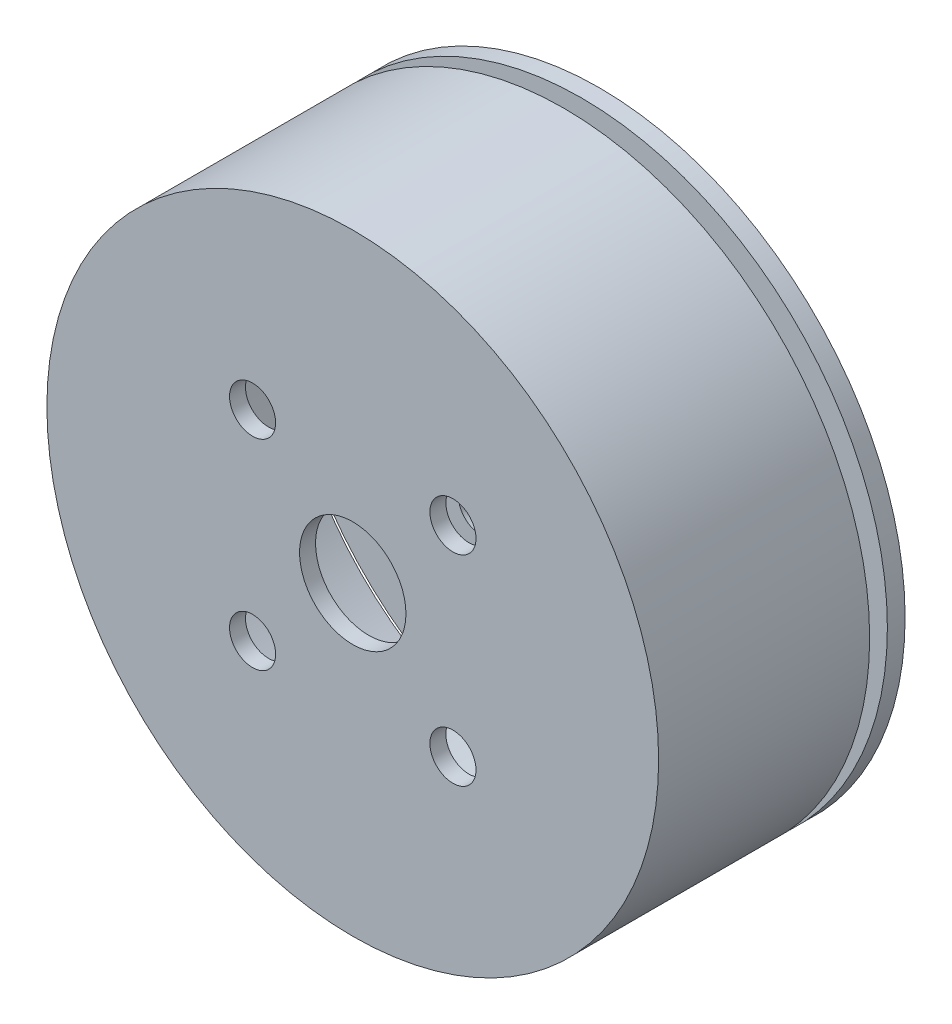
SolidWorks part; units mm, degrees
ref_plane "前视基准面" through (0, 0, 0) normal (0, 0, 1) x (1, 0, 0)
ref_plane "上视基准面" through (0, 0, 0) normal (0, 1, 0) x (1, 0, 0)
ref_plane "右视基准面" through (0, 0, 0) normal (1, 0, 0) x (0, 0, -1)
sketch "草图1" plane through (0, 0, 0) normal (0, 0, 1) x (1, 0, 0)
  circle A0 centre (0, 0) radius 17.25
  dimension "D1" = 34.5
extrude "凸台-拉伸1" add sketch "草图1" along normal blind 13.9
ref_plane "基准面4" through (0, 0, 1) normal (0, 0, -1) x (-1, 0, 0)
sketch "草图3" plane through (0, 0, 1) normal (0, 0, -1) x (-1, 0, 0)
  circle A0 centre (0, 0) radius 17.25
extrude "切除-拉伸2" cut sketch "草图3" against normal blind 1
sketch "草图4" plane through (0, 0, 2) normal (0, 0, -1) x (-1, 0, 0)
  circle A2 centre (0, 0) radius 16
  dimension "D1" = 32
extrude "切除-拉伸4" cut sketch "草图4" against normal blind 11
sketch "草图5" plane through (0, 0, 13.9) normal (0, 0, 1) x (1, 0, 0)
  line L5 (-5.65, -5.65) -> (5.65, 5.65) construction
  line L6 (-5.65, 5.65) -> (5.65, -5.65) construction
  circle A0 centre (5.65, 5.65) radius 1.3
  circle A1 centre (5.65, -5.65) radius 1.3
  circle A2 centre (-5.65, -5.65) radius 1.3
  circle A3 centre (-5.65, 5.65) radius 1.3
  circle A4 centre (0, 0) radius 3
  point P0 (0, 0)
  dimension "D2" = 2.6
  dimension "D3" = 2.6
  dimension "D4" = 2.6
  dimension "D5" = 2.6
  dimension "D6" = 6
  dimension "D1" = 11.3
extrude "切除-拉伸5" cut sketch "草图5" along direction (0, 0, 1) on the side against the normal blind 15
sketch "草图6" plane through (0, 0, 0) normal (0, 0, -1) x (-1, 0, 0)
  line L5 (-5.65, -5.65) -> (5.65, 5.65) construction
  line L6 (-5.65, 5.65) -> (5.65, -5.65) construction
  circle A0 centre (-5.65, 5.65) radius 1.3
  circle A1 centre (5.65, 5.65) radius 1.3
  circle A2 centre (5.65, -5.65) radius 1.3
  circle A3 centre (-5.65, -5.65) radius 1.3
  circle A4 centre (0, 0) radius 3
  point P0 (0, 0)
  dimension "D2" = 2.6
  dimension "D3" = 2.6
  dimension "D4" = 2.6
  dimension "D5" = 2.6
  dimension "D6" = 6
  dimension "D1" = 11.3
extrude "切除-拉伸6" cut sketch "草图6" against normal blind 10
